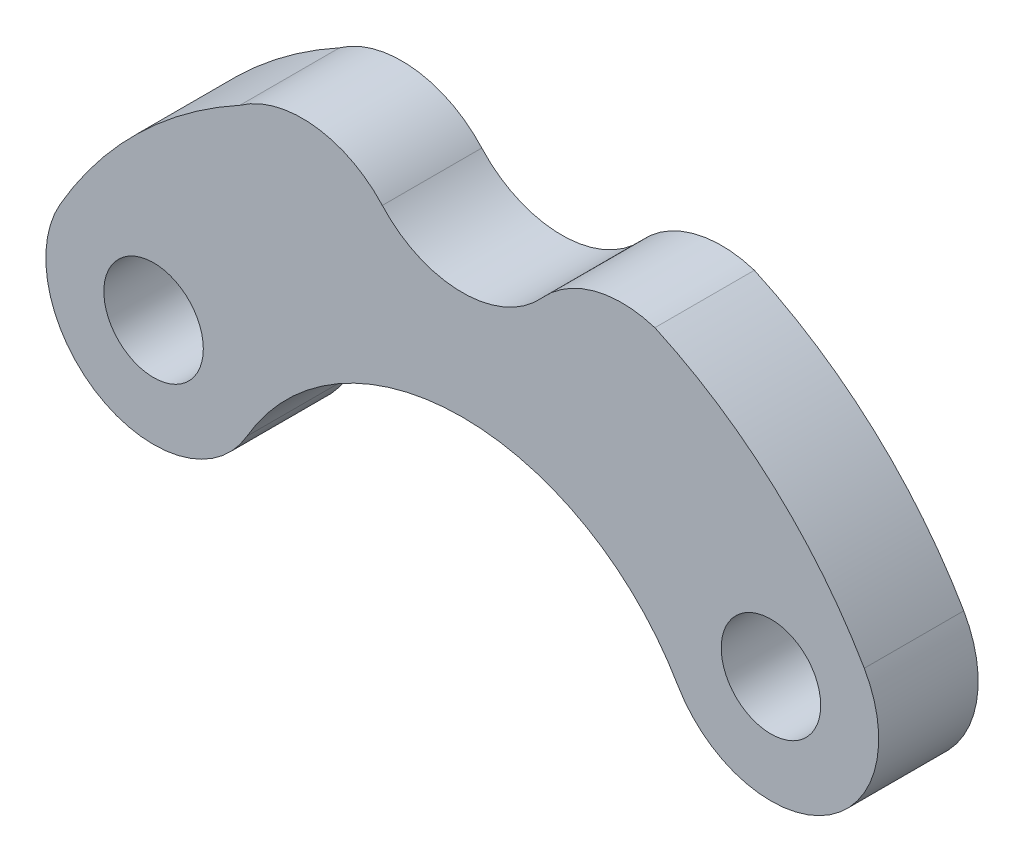
SolidWorks part; units mm, degrees
ref_plane "Plan de face" through (0, 0, 0) normal (0, 0, 1) x (1, 0, 0)
ref_plane "Plan de dessus" through (0, 0, 0) normal (0, 1, 0) x (1, 0, 0)
ref_plane "Plan de droite" through (0, 0, 0) normal (1, 0, 0) x (0, 0, -1)
sketch "Esquisse1" plane through (0, 0, 0) normal (0, 0, 1) x (1, 0, 0)
  line L0 (9.3098, 5.375) -> (7.6848, 2.5604) construction
  line L2 (-9.3098, 5.375) -> (9.3098, 5.375) construction
  line L4 (-7.6848, 2.5604) -> (-9.3098, 5.375) construction
  arc A12 (-2.411, 11.8207) -> (2.411, 11.8207) centre (0, 14) ccw
  arc A16 (5.8094, 12.7378) -> (2.411, 11.8207) centre (4.8221, 9.6414) ccw
  arc A17 (-2.411, 11.8207) -> (-6.7074, 12.2887) centre (-4.8221, 9.6414) ccw
  arc A18 (-6.7074, 12.2887) -> (-12.1244, 7) centre (0, 0) ccw
  arc A28 (12.1244, 7) -> (5.8094, 12.7378) centre (0, 0) ccw
  arc A30 (10.4906, 2.3471) -> (-10.4906, 2.3471) centre (0, 0) ccw construction
  circle A31 centre (9.3098, 5.375) radius 1.5
  circle A33 centre (-9.3098, 5.375) radius 1.5
  arc A34 (6.4952, 3.75) -> (12.1244, 7) centre (9.3098, 5.375) ccw
  arc A35 (-12.1244, 7) -> (-6.4952, 3.75) centre (-9.3098, 5.375) ccw
  arc A37 (6.4952, 3.75) -> (-6.4952, 3.75) centre (0, 0) ccw
  point P31 (0, 0)
  dimension "D3" = 6.5
  dimension "D8" = 14
  dimension "D9" = 3.25
  dimension "D10" = 6.5
  dimension "D11" = 3.25
  dimension "D7" = 60
  dimension "D14" = 10.78
  dimension "D15" = 10.78
extrude "Boss.-Extru.2" add sketch "Esquisse1" along normal blind 3
